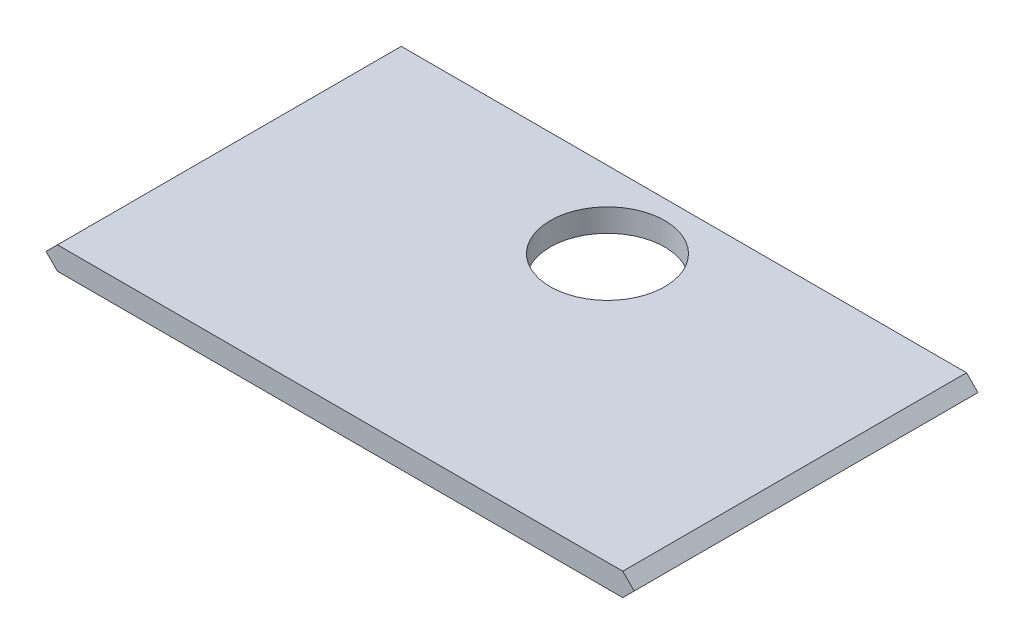
SolidWorks part; units mm, degrees
ref_plane "Plan de face" through (0, 0, 0) normal (0, 0, 1) x (1, 0, 0)
ref_plane "Plan de dessus" through (0, 0, 0) normal (0, 1, 0) x (1, 0, 0)
ref_plane "Plan de droite" through (0, 0, 0) normal (1, 0, 0) x (0, 0, -1)
sketch "Esquisse1" plane through (0, 0, 0) normal (0, 0, 1) x (1, 0, 0)
  line L0 (0, 0) -> (74, 0)
  line L1 (74, 0) -> (75.5, 1.5)
  line L2 (75.5, 1.5) -> (74, 3)
  line L3 (74, 3) -> (0, 3)
  line L4 (0, 3) -> (-1.5, 1.5)
  line L5 (-1.5, 1.5) -> (0, 0)
  dimension "D1" = 90
  dimension "D2" = 135
  dimension "D3" = 135
  dimension "D4" = 3
  dimension "D5" = 0
  dimension "D6" = 74
  dimension "D7" = 74
  dimension "D8" = 135
  dimension "D9" = 135
extrude "Boss.-Extru.1" add sketch "Esquisse1" along normal blind 45
sketch "Esquisse2" plane through (0, 3, 0) normal (0, 1, 0) x (1, 0, 0)
  line L0 (74, 0) -> (0, 0) construction
  line L1 (75.5, -45) -> (75.5, 0) construction
  line L2 (-1.5, -45) -> (-1.5, 0) construction
  circle A0 centre (37, -10) radius 7.5
  dimension "D1" = 15
  dimension "D2" = 10
  dimension "D3" = 38.5
  dimension "D4" = 38.5
extrude "Enlèv. mat.-Extru.1" cut sketch "Esquisse2" against normal through all
